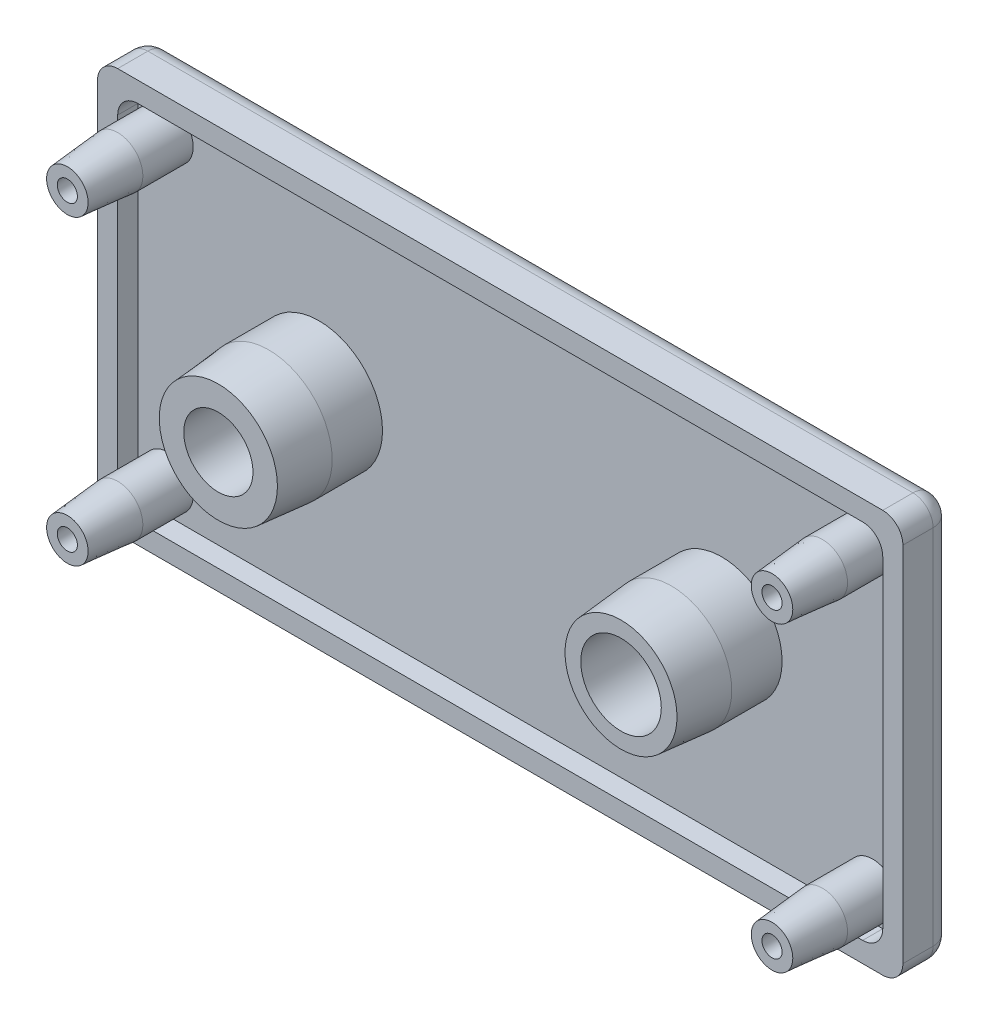
SolidWorks part; units mm, degrees
ref_plane "前视基准面" through (0, 0, 0) normal (0, 0, 1) x (1, 0, 0)
ref_plane "上视基准面" through (0, 0, 0) normal (0, 1, 0) x (1, 0, 0)
ref_plane "右视基准面" through (0, 0, 0) normal (1, 0, 0) x (0, 0, -1)
sketch "草图1" plane through (0, 0, 0) normal (0, 0, 1) x (1, 0, 0)
  line L1 (-45.3725, 19.904) -> (34.6275, 19.904)
  line L2 (-45.3725, 19.904) -> (-45.3725, -20.096)
  line L3 (-45.3725, -20.096) -> (34.6275, -20.096)
  line L4 (34.6275, 19.904) -> (34.6275, -20.096)
  dimension "D1" = 80
  dimension "D2" = 40
extrude "拉伸1" add sketch "草图1" along normal blind 5
fillet "圆角1" radius 2 4 edges at (-45.3725, -20.096, 2.5) (34.6275, -20.096, 2.5) (34.6275, 19.904, 2.5) (-45.3725, 19.904, 2.5)
sketch "草图2" plane through (0, 0, 5) normal (0, 0, 1) x (1, 0, 0)
  line L0 (-45.3725, 17.904) -> (-45.3725, -18.096) construction
  line L1 (-43.3725, 17.904) -> (32.6275, 17.904)
  line L2 (-43.3725, 17.904) -> (-43.3725, -18.096)
  line L3 (-43.3725, -18.096) -> (32.6275, -18.096)
  line L4 (32.6275, 17.904) -> (32.6275, -18.096)
  line L5 (32.6275, 19.904) -> (-43.3725, 19.904) construction
  dimension "D1" = 76
  dimension "D2" = 36
  dimension "D3" = 2
  dimension "D4" = 2
extrude "切除-拉伸1" cut sketch "草图2" against normal blind 2
fillet "圆角2" radius 2 4 edges at (32.6275, -18.096, 4) (-43.3725, -18.096, 4) (32.6275, 17.904, 4) (-43.3725, 17.904, 4)
fillet "圆角3" radius 2 8 edges at (34.0417, -19.5102, 0) (34.6275, -0.096, 0) (34.0417, 19.3182, 0) (-5.3725, 19.904, 0) (-44.7867, 19.3182, 0) (-45.3725, -0.096, 0) (-44.7867, -19.5102, 0) (-5.3725, -20.096, 0)
sketch "草图3" plane through (0, 0, 3) normal (0, 0, 1) x (1, 0, 0)
  line L0 (-45.3725, 17.904) -> (-45.3725, -18.096) construction
  line L1 (-43.3725, -20.096) -> (32.6275, -20.096) construction
  line L2 (32.6275, 19.904) -> (-43.3725, 19.904) construction
  line L3 (34.6275, -18.096) -> (34.6275, 17.904) construction
  circle A0 centre (-40.3725, 14.904) radius 2.5
  circle A1 centre (29.6275, 14.904) radius 2.5
  circle A2 centre (29.6275, -15.096) radius 2.5
  circle A3 centre (-40.3725, -15.096) radius 2.5
  circle A4 centre (14.6275, -0.096) radius 6
  circle A5 centre (-40.3725, 14.904) radius 1
  circle A6 centre (14.6275, -0.096) radius 4
  circle A7 centre (-40.3725, -15.096) radius 1
  circle A8 centre (29.6275, 14.904) radius 1
  circle A9 centre (29.6275, -15.096) radius 1
  dimension "D1" = 5
  dimension "D2" = 5
  dimension "D3" = 5
  dimension "D4" = 5
  dimension "D5" = 12
  dimension "D6" = 2
  dimension "D7" = 2
  dimension "D8" = 2
  dimension "D9" = 2
  dimension "D10" = 8
  dimension "D11" = 5
  dimension "D12" = 5
  dimension "D13" = 5
  dimension "D14" = 5
  dimension "D15" = 5
  dimension "D16" = 5
  dimension "D17" = 5
  dimension "D18" = 5
  dimension "D19" = 20
  dimension "D20" = 20
extrude "拉伸2" add sketch "草图3" along normal blind 10
chamfer "倒角1" distance 5 angle 5 1 edges at (20.6275, -0.096, 13)
sketch "草图4" plane through (0, 0, 3) normal (0, 0, 1) x (1, 0, 0)
  line L0 (32.6275, 19.904) -> (-43.3725, 19.904) construction
  line L1 (-45.3725, 17.904) -> (-45.3725, -18.096) construction
  circle A0 centre (-25.3725, -0.096) radius 6.3067
  circle A1 centre (-25.3725, -0.096) radius 3.4385
  dimension "D1" = 20
  dimension "D2" = 20
extrude "拉伸3" add sketch "草图4" along normal blind 10
chamfer "倒角2" distance 5 angle 5 1 edges at (-19.0658, -0.096, 13)
chamfer "倒角4" distance 5 angle 5 4 edges at (32.1275, -15.096, 13) (32.1275, 14.904, 13) (-37.8725, -15.096, 13) (-37.8725, 14.904, 13)
